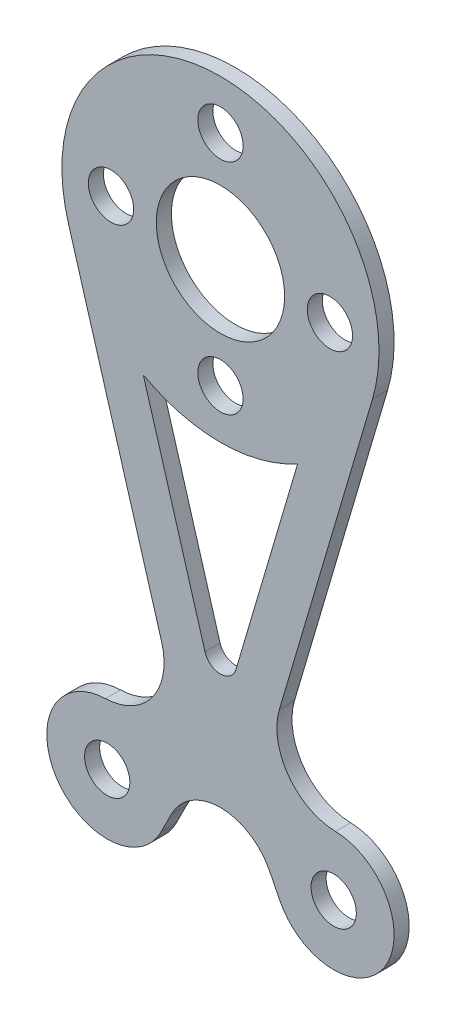
SolidWorks part; units mm, degrees
ref_plane "前视基准面" through (0, 0, 0) normal (0, 0, 1) x (1, 0, 0)
ref_plane "上视基准面" through (0, 0, 0) normal (0, 1, 0) x (1, 0, 0)
ref_plane "右视基准面" through (0, 0, 0) normal (1, 0, 0) x (0, 0, -1)
sketch "草图1" plane through (0, 0, 0) normal (0, 0, 1) x (1, 0, 0)
  line L0 (-7.5, 0) -> (7.5, 0) construction
  line L1 (0, 0) -> (0, 33) construction
  line L2 (-10.0702, 30.0267) -> (-3.9, 9.1292)
  line L3 (-3.9229, -1.79) -> (-3.2516, -0.4486)
  line L4 (10.0702, 30.0267) -> (3.9, 9.1292)
  line L5 (3.2516, -0.4486) -> (3.9229, -1.79)
  line L6 (-14.0972, 33) -> (14.6342, 33) construction
  line L7 (-5.1121, 23.8285) -> (-1.0228, 9.9787)
  line L8 (5.1121, 23.8285) -> (1.0228, 9.9787)
  line L9 (-7.193, 30.8762) -> (-1.0228, 9.9787) construction
  line L10 (7.193, 30.8762) -> (1.0228, 9.9787) construction
  circle A0 centre (-7.5, 0) radius 1.5
  circle A1 centre (7.5, 0) radius 1.5
  arc A2 (10.0702, 30.0267) -> (-10.0702, 30.0267) centre (0, 33) ccw
  circle A3 centre (0, 33) radius 4.25
  arc A4 (-7.6181, 3.9983) -> (-3.9229, -1.79) centre (-7.5, 0) ccw
  arc A5 (3.9229, -1.79) -> (7.6181, 3.9983) centre (7.5, 0) ccw
  arc A6 (-3.9, 9.1292) -> (-7.6181, 3.9983) centre (-7.7363, 7.9965) cw
  arc A7 (3.9, 9.1292) -> (7.6181, 3.9983) centre (7.7363, 7.9965) ccw
  arc A8 (-3.2516, -0.4486) -> (3.2516, -0.4486) centre (0, -2.0757) cw
  circle A9 centre (0, 33) radius 7.25 construction
  circle A10 centre (0, 40.25) radius 1.5
  circle A11 centre (-7.25, 33) radius 1.5
  circle A12 centre (0, 25.75) radius 1.5
  circle A13 centre (7.25, 33) radius 1.5
  arc A14 (-5.1121, 23.8285) -> (5.1121, 23.8285) centre (0, 33) ccw
  arc A15 (-1.0228, 9.9787) -> (1.0228, 9.9787) centre (0, 10.2807) ccw
  dimension "D2" = 3
  dimension "D3" = 3
  dimension "D5" = 21
  dimension "D6" = 8.5
  dimension "D7" = 2.5
  dimension "D8" = 8
  dimension "D9" = 4
  dimension "D13" = 3
  dimension "D14" = 14.5
  dimension "D1" = 15
  dimension "D4" = 33
  dimension "D11" = 7.8
  dimension "D12" = 1.5
  dimension "D15" = 7.5
  dimension "D16" = 7.5
  dimension "D17" = 3
  dimension "D18" = 3
extrude "凸台-拉伸1" add sketch "草图1" along normal blind 1
